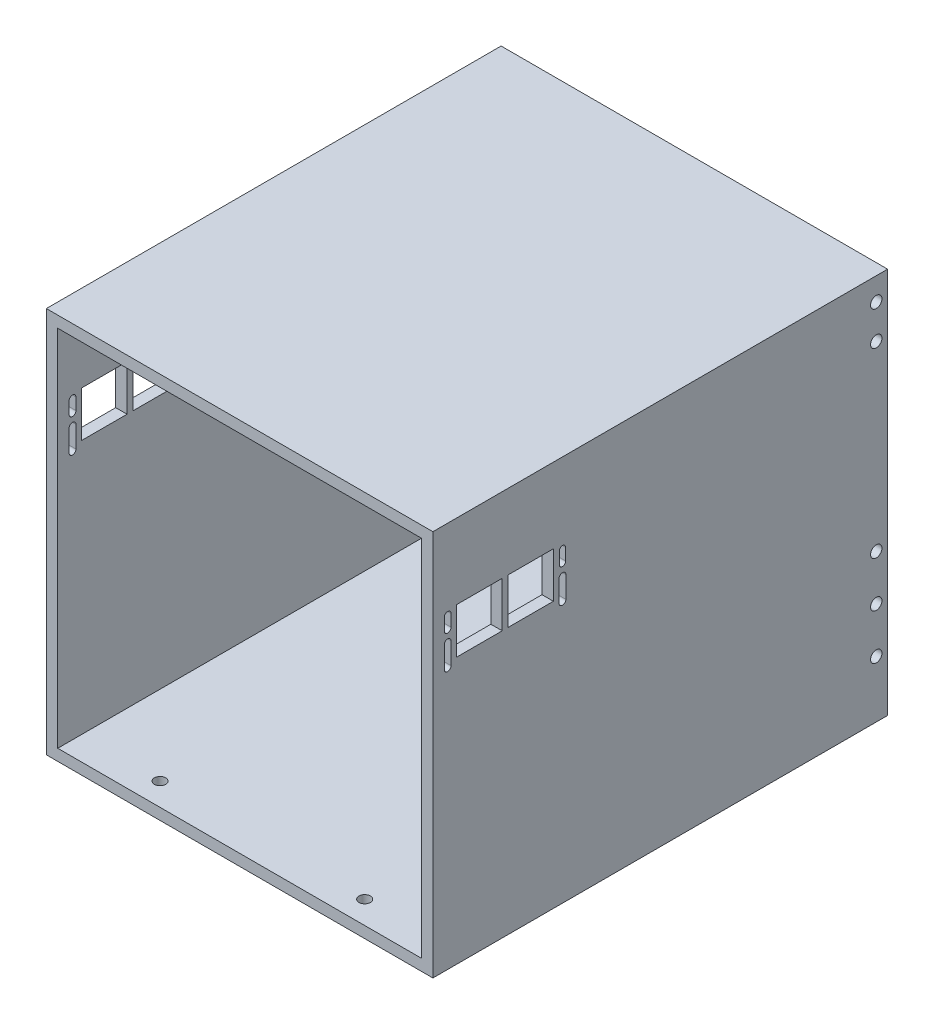
SolidWorks part; units mm, degrees
material "PE High Density"
ref_plane "Front Plane" through (0, 0, 0) normal (0, 0, 1) x (1, 0, 0)
ref_plane "Top Plane" through (0, 0, 0) normal (0, 1, 0) x (1, 0, 0)
ref_plane "Right Plane" through (0, 0, 0) normal (1, 0, 0) x (0, 0, -1)
sketch "Sketch1" plane through (0, 0, 0) normal (0, 0, 1) x (1, 0, 0)
  line L1 (101.6, -101.6) -> (-101.6, -101.6)
  line L2 (101.6, -101.6) -> (101.6, 101.6)
  line L3 (101.6, 101.6) -> (-101.6, 101.6)
  line L4 (-101.6, -101.6) -> (-101.6, 101.6)
  line L5 (101.6, -101.6) -> (-101.6, 101.6) construction
  line L6 (101.6, 101.6) -> (-101.6, -101.6) construction
  line L7 (107.95, -107.95) -> (-107.95, -107.95)
  line L8 (107.95, -107.95) -> (107.95, 107.95)
  line L9 (107.95, 107.95) -> (-107.95, 107.95)
  line L10 (-107.95, -107.95) -> (-107.95, 107.95)
  line L11 (107.95, -107.95) -> (-107.95, 107.95) construction
  line L12 (107.95, 107.95) -> (-107.95, -107.95) construction
  point P0 (0, 0)
  point P6 (0, 0)
  dimension "D1" = 6.35
  dimension "D2" = 6.35
  dimension "D3" = 203.2
  dimension "D4" = 203.2
extrude "Boss-Extrude1" add sketch "Sketch1" along normal blind 254
sketch "Sketch2" plane through (107.95, 0, 0) normal (1, 0, 0) x (0, 0, -1)
  line L0 (-254, -107.95) -> (-254, 107.95) construction
  line L1 (-240.6768, 66.04) -> (-215.2768, 66.04)
  line L2 (-240.6768, 66.04) -> (-240.6768, 40.64)
  line L3 (-240.6768, 40.64) -> (-215.2768, 40.64)
  line L4 (-215.2768, 66.04) -> (-215.2768, 40.64)
  line L5 (-212.1018, 66.04) -> (-186.7018, 66.04)
  line L6 (-212.1018, 66.04) -> (-212.1018, 40.64)
  line L7 (-254, 107.95) -> (0, 107.95) construction
  line L12 (-212.1018, 40.64) -> (-186.7018, 40.64)
  line L13 (-186.7018, 66.04) -> (-186.7018, 40.64)
  line L14 (-254, -101.6) -> (0, -101.6) construction
  line L15 (0, -107.95) -> (0, 107.95) construction
  line L28 (0, -101.6) -> (-254, -101.6) construction
  line L29 (-245.7509, 50.0534) -> (-245.7509, 38.0646) construction
  line L30 (-243.8518, 50.0534) -> (-243.8518, 38.0646)
  line L31 (-247.65, 50.0534) -> (-247.65, 38.0646)
  line L32 (-245.7509, 56.6828) -> (-245.7509, 63.2871) construction
  line L33 (-247.65, 56.6828) -> (-247.65, 63.2871)
  line L34 (-243.8518, 56.6828) -> (-243.8518, 63.2871)
  line L35 (-181.6277, 50.0534) -> (-181.6277, 38.0646) construction
  line L36 (-179.7286, 50.0534) -> (-179.7286, 38.0646)
  line L37 (-183.5268, 50.0534) -> (-183.5268, 38.0646)
  line L38 (-181.6277, 56.6828) -> (-181.6277, 63.2871) construction
  line L39 (-183.4057, 56.6828) -> (-183.4057, 63.2871)
  line L40 (-179.8497, 56.6828) -> (-179.8497, 63.2871)
  circle A24 centre (-526.4826, -12.7) radius 88.9 construction
  circle A25 centre (-348.6826, -12.7) radius 88.9 construction
  arc A26 (-243.8518, 50.0534) -> (-247.65, 50.0534) centre (-245.7509, 50.0534) ccw
  arc A27 (-247.65, 38.0646) -> (-243.8518, 38.0646) centre (-245.7509, 38.0646) ccw
  arc A28 (-247.65, 56.6828) -> (-243.8518, 56.6828) centre (-245.7509, 56.6828) ccw
  arc A29 (-243.8518, 63.2871) -> (-247.65, 63.2871) centre (-245.7509, 63.2871) ccw
  arc A30 (-179.7286, 50.0534) -> (-183.5268, 50.0534) centre (-181.6277, 50.0534) ccw
  arc A31 (-183.5268, 38.0646) -> (-179.7286, 38.0646) centre (-181.6277, 38.0646) ccw
  arc A32 (-183.4057, 56.6828) -> (-179.8497, 56.6828) centre (-181.6277, 56.6828) ccw
  arc A33 (-179.8497, 63.2871) -> (-183.4057, 63.2871) centre (-181.6277, 63.2871) ccw
  point P10 (-348.6826, -12.7)
  point P17 (-245.7509, 44.059)
  point P23 (-245.7509, 59.9849)
  point P35 (-181.6277, 44.059)
  point P40 (-181.6277, 59.9849)
  point P49 (0, 0)
  point P50 (0, 0)
  point P55 (0, 0)
  dimension "D4" = 25.4
  dimension "D5" = 25.4
  dimension "D7" = 25.4
  dimension "D6" = 25.4
  dimension "D8" = 6.6043
  dimension "D17" = 6.35
  dimension "D13" = 1.778
  dimension "D14" = 1.8991
  dimension "D15" = 3.175
  dimension "D9" = 3.175
  dimension "D11" = 1.8991
  dimension "D16" = 3.175
  dimension "D18" = 177.8
  dimension "D12" = 1.8991
  dimension "D2" = 3.175
  dimension "D3" = 142.24
  dimension "D10" = 6.6294
  dimension "D19" = 2.7529
  dimension "D20" = 2.5754
extrude "Cut-Extrude1" cut sketch "Sketch2" against normal through all
sketch "Sketch5" plane through (0, -107.95, 0) normal (0, -1, 0) x (1, 0, 0)
  line L0 (-107.95, 254) -> (-107.95, 0) construction
  line L1 (-107.95, 0) -> (107.95, 0) construction
  circle A0 centre (-76.2, 6.35) radius 3.175
  circle A1 centre (-50.8, 6.35) radius 3.175
  circle A2 centre (0, 6.35) radius 3.175
  circle A3 centre (25.4, 6.35) radius 3.175
  dimension "D1" = 6.35
  dimension "D6" = 6.35
  dimension "D2" = 31.75
  dimension "D3" = 25.4
  dimension "D4" = 50.8
  dimension "D5" = 25.4
extrude "Cut-Extrude4" cut sketch "Sketch5" against normal blind 6.35
sketch "Sketch6" plane through (107.95, 0, 0) normal (1, 0, 0) x (0, 0, -1)
  line L1 (0, -107.95) -> (0, 107.95) construction
  line L2 (-254, -107.95) -> (0, -107.95) construction
  line L3 (-254, 107.95) -> (0, 107.95) construction
  circle A0 centre (-6.35, 95.25) radius 3.1801
  circle A1 centre (-6.35, 76.2) radius 3.1801
  circle A3 centre (-6.35, -25.4) radius 3.1801
  circle A4 centre (-6.35, -50.8) radius 3.1801
  circle A5 centre (-6.35, -76.2) radius 3.1801
  dimension "D2" = 6.3602
  dimension "D3" = 19.05
  dimension "D1" = 12.7
  dimension "D4" = 25.4
  dimension "D5" = 6.35
  dimension "D7" = 31.75
  dimension "D6" = 25.4
  dimension "D8" = 6.35
extrude "Cut-Extrude5" cut sketch "Sketch6" against normal through all
sketch "Sketch7" plane through (0, -101.6, 0) normal (0, 1, 0) x (1, 0, 0)
  line L0 (-107.95, -254) -> (-107.95, 0) construction
  line L1 (107.95, -254) -> (107.95, 0) construction
  line L2 (-101.6, -254) -> (101.6, -254) construction
  circle A0 centre (-57.15, -241.3) radius 3.175
  circle A1 centre (57.15, -241.3) radius 3.175
  dimension "D5" = 6.35
  dimension "D6" = 6.35
  dimension "D1" = 50.8
  dimension "D2" = 50.8
  dimension "D3" = 12.7
  dimension "D4" = 12.7
extrude "Cut-Extrude6" cut sketch "Sketch7" against normal blind 12.7
